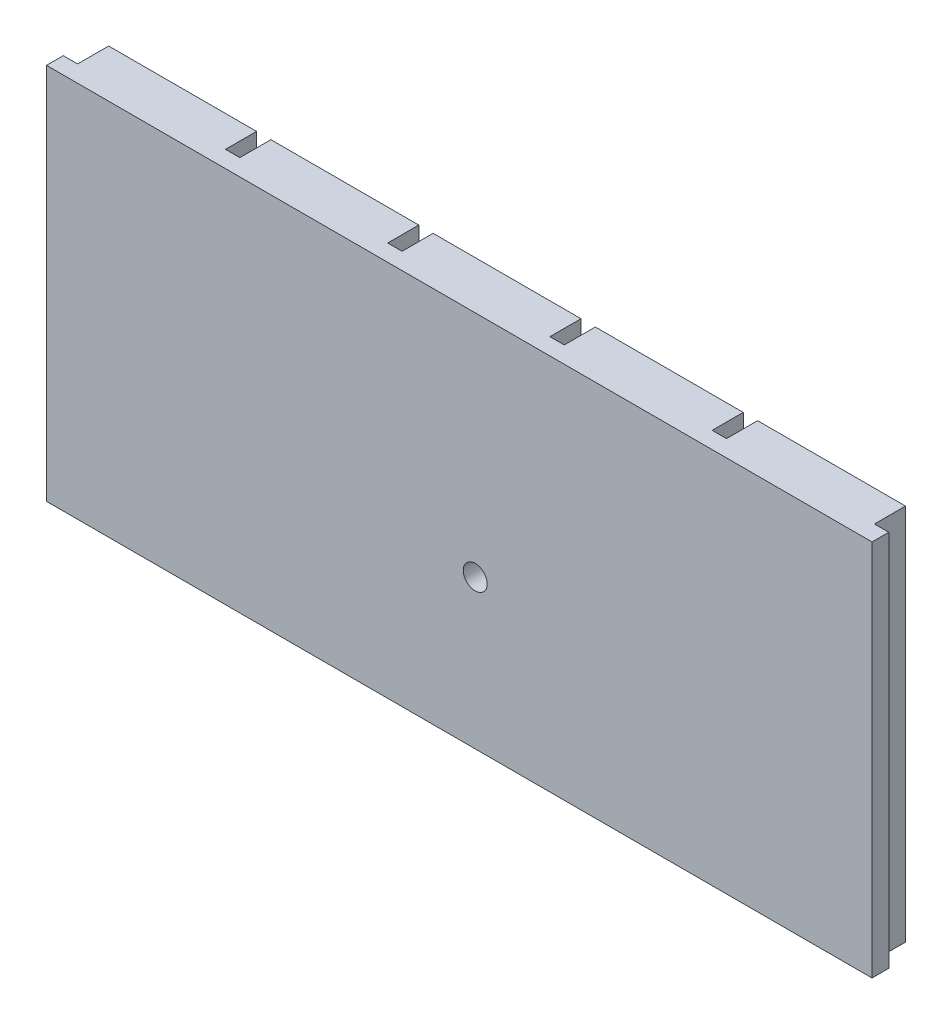
SolidWorks part; units mm, degrees
ref_plane "Front" through (0, 0, 0) normal (0, 0, 1) x (1, 0, 0)
ref_plane "Top" through (0, 0, 0) normal (0, 1, 0) x (1, 0, 0)
ref_plane "Right" through (0, 0, 0) normal (1, 0, 0) x (0, 0, -1)
sketch "Sketch1" plane through (0, 0, 0) normal (0, 0, 1) x (1, 0, 0)
  line L0 (86.3442, 0) -> (-86.3442, 0) construction
  line L1 (-86.3442, -39.5) -> (86.3442, -39.5)
  line L2 (-86.3442, -39.5) -> (-86.3442, 39.5)
  line L3 (-86.3442, 39.5) -> (86.3442, 39.5)
  line L4 (86.3442, -39.5) -> (86.3442, 39.5)
  line L5 (-86.3442, -39.5) -> (86.3442, 39.5) construction
  line L6 (-86.3442, 39.5) -> (86.3442, -39.5) construction
  line L9 (88.3442, -41) -> (88.3442, 38) construction
  circle A0 centre (3.3372, -8.3868) radius 2.5
  circle A1 centre (3.3372, -8.3868) radius 2.5 construction
  point P0 (0, 0)
extrude "Boss-Extrude1" add sketch "Sketch1" along normal blind 10
sketch "Sketch2" plane through (0, 39.5, 0) normal (0, 1, 0) x (1, 0, 0)
  line L0 (86.3442, 0) -> (-86.3442, 0) construction
  line L1 (86.3442, 0) -> (86.3442, -6.5)
  line L2 (86.3442, 0) -> (83.3442, 0)
  line L3 (86.3442, -6.5) -> (83.3442, -6.5)
  line L4 (83.3442, 0) -> (83.3442, -6.5)
  line L5 (86.3442, -10) -> (86.3442, 0) construction
  line L6 (52.4065, 0) -> (52.4065, -6.5)
  line L7 (52.4065, 0) -> (49.4065, 0)
  line L8 (52.4065, -6.5) -> (49.4065, -6.5)
  line L9 (49.4065, 0) -> (49.4065, -6.5)
  line L10 (18.4688, 0) -> (18.4688, -6.5)
  line L11 (18.4688, 0) -> (15.4688, 0)
  line L12 (18.4688, -6.5) -> (15.4688, -6.5)
  line L13 (15.4688, 0) -> (15.4688, -6.5)
  line L14 (-15.4688, 0) -> (-15.4688, -6.5)
  line L15 (-15.4688, 0) -> (-18.4688, 0)
  line L16 (-15.4688, -6.5) -> (-18.4688, -6.5)
  line L17 (-18.4688, 0) -> (-18.4688, -6.5)
  line L18 (-49.4065, 0) -> (-49.4065, -6.5)
  line L19 (-49.4065, 0) -> (-52.4065, 0)
  line L20 (-49.4065, -6.5) -> (-52.4065, -6.5)
  line L21 (-52.4065, 0) -> (-52.4065, -6.5)
  line L22 (-83.3442, 0) -> (-83.3442, -6.5)
  line L23 (-83.3442, 0) -> (-86.3442, 0)
  line L24 (-83.3442, -6.5) -> (-86.3442, -6.5)
  line L25 (-86.3442, 0) -> (-86.3442, -6.5)
  line L26 (-86.3442, -10) -> (-86.3442, 0) construction
  dimension "D1" = 6.5
  dimension "D3" = 3
  dimension "D2" = 6
extrude "Cut-Extrude1" cut sketch "Sketch2" against normal up to next
